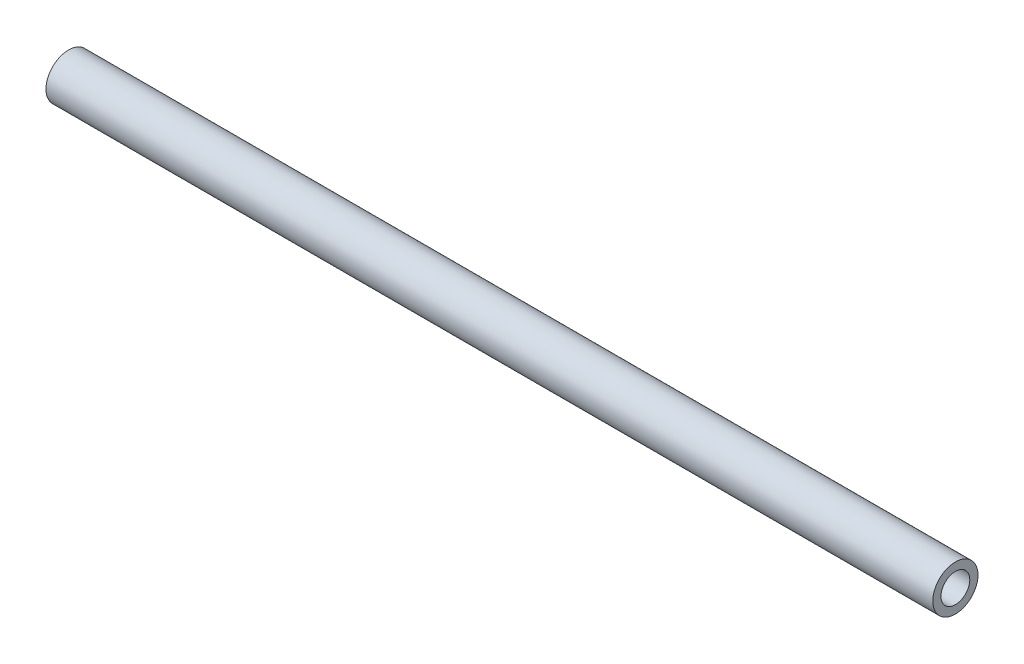
SolidWorks part; units mm, degrees
ref_plane "Front Plane" through (0, 0, 0) normal (0, 0, 1) x (1, 0, 0)
ref_plane "Top Plane" through (0, 0, 0) normal (0, 1, 0) x (1, 0, 0)
ref_plane "Right Plane" through (0, 0, 0) normal (1, 0, 0) x (0, 0, -1)
sketch "Sketch1" plane through (0, 0, 0) normal (1, 0, 0) x (0, 0, -1)
  circle A0 centre (0, 0) radius 5.1
  circle A1 centre (0, 0) radius 3.25
  dimension "D1" = 6.5
  dimension "D2" = 10.2
extrude "Boss-Extrude1" add sketch "Sketch1" along normal blind 200
